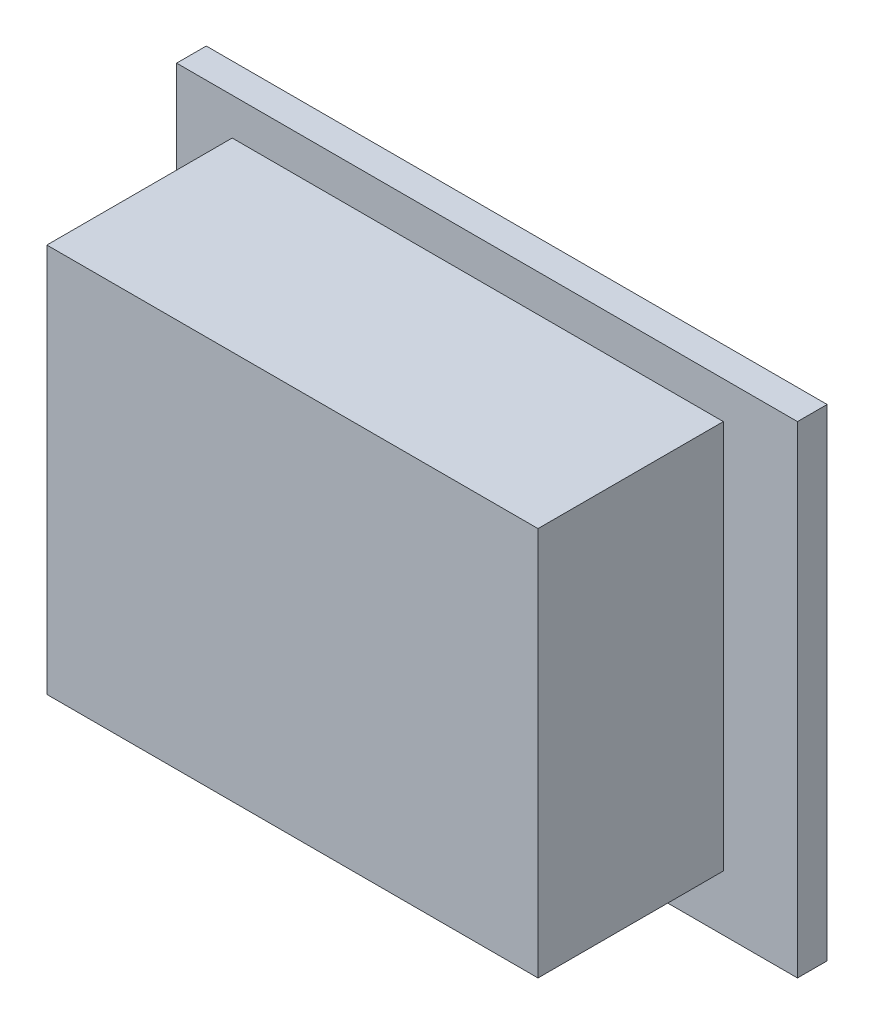
SolidWorks part; units mm, degrees
ref_plane "Plan de face" through (0, 0, 0) normal (0, 0, 1) x (1, 0, 0)
ref_plane "Plan de dessus" through (0, 0, 0) normal (0, 1, 0) x (1, 0, 0)
ref_plane "Plan de droite" through (0, 0, 0) normal (1, 0, 0) x (0, 0, -1)
sketch "Esquisse1" plane through (0, 0, 0) normal (0, 0, 1) x (1, 0, 0)
  line L1 (0, 0) -> (33.5, 0)
  line L2 (0, 0) -> (0, 26)
  line L3 (0, 26) -> (33.5, 26)
  line L4 (33.5, 0) -> (33.5, 26)
  dimension "D1" = 26
  dimension "D2" = 33.5
extrude "Boss.-Extru.1" add sketch "Esquisse1" along normal blind 1.6
sketch "Esquisse2" plane through (0, 0, 1.6) normal (0, 0, 1) x (1, 0, 0)
  line L0 (33.5, 26) -> (0, 26) construction
  line L1 (3, 3) -> (29.5, 3)
  line L2 (3, 3) -> (3, 24)
  line L3 (3, 24) -> (29.5, 24)
  line L4 (29.5, 3) -> (29.5, 24)
  line L6 (0, 26) -> (0, 0) construction
  line L8 (33.5, 0) -> (33.5, 26) construction
  dimension "D1" = 21
  dimension "D2" = 2
  dimension "D3" = 3
  dimension "D4" = 4
extrude "Boss.-Extru.2" add sketch "Esquisse2" along normal blind 10
